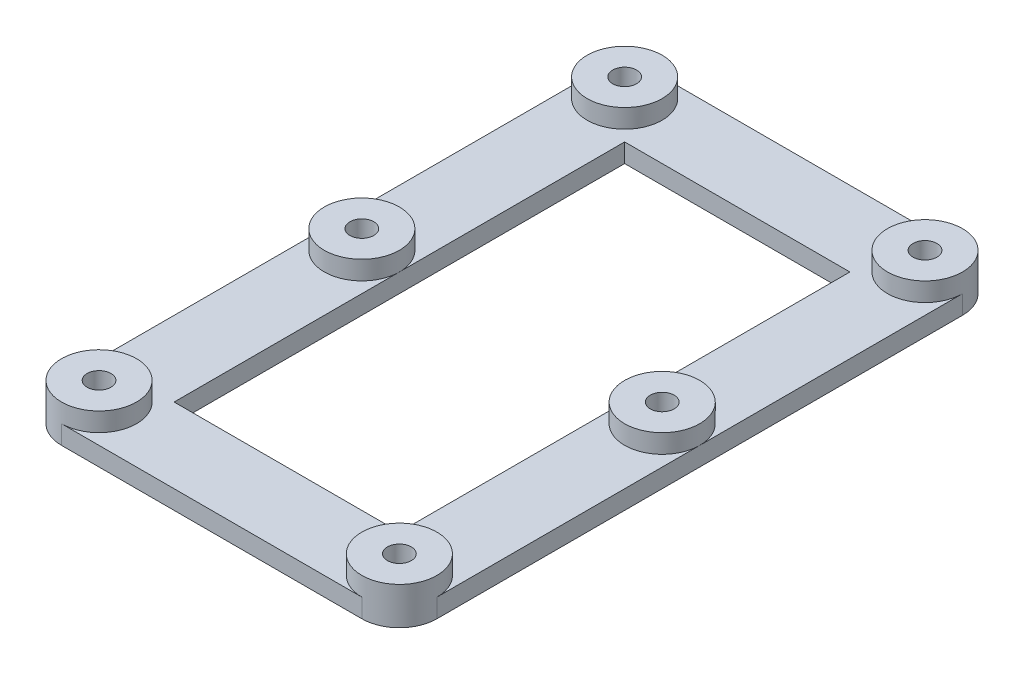
SolidWorks part; units mm, degrees
material "5052-H32"
ref_plane "Front Plane" through (0, 0, 0) normal (0, 0, 1) x (1, 0, 0)
ref_plane "Top Plane" through (0, 0, 0) normal (0, 1, 0) x (1, 0, 0)
ref_plane "Right Plane" through (0, 0, 0) normal (1, 0, 0) x (0, 0, -1)
sketch "Sketch1" plane through (0, 0, 0) normal (0, 1, 0) x (1, 0, 0)
  line L1 (31.75, -50.8) -> (-31.75, -50.8)
  line L2 (31.75, -50.8) -> (31.75, 50.8)
  line L3 (31.75, 50.8) -> (-31.75, 50.8)
  line L4 (-31.75, -50.8) -> (-31.75, 50.8)
  line L5 (31.75, -50.8) -> (-31.75, 50.8) construction
  line L6 (31.75, 50.8) -> (-31.75, -50.8) construction
  point P0 (0, 0)
  dimension "D1" = 101.6
  dimension "D2" = 63.5
extrude "Boss-Extrude1" add sketch "Sketch1" along normal blind 6.35
fillet "Fillet1" radius 6.35 4 edges at (31.75, 3.175, -50.8) (31.75, 3.175, 50.8) (-31.75, 3.175, 50.8) (-31.75, 3.175, -50.8)
hole_wizard "#10-32 Tapped Hole1" positions "Sketch8" profile "Sketch9" tap size "#10-32" standard "ANSI Inch" end condition through all
sketch "Sketch8" plane through (0, 6.35, 0) normal (0, 1, 0) x (1, 0, 0)
  line L0 (25.4, 44.45) -> (-25.4, 44.45)
  line L1 (-25.4, 44.45) -> (-25.4, -44.45)
  line L2 (-25.4, -44.45) -> (25.4, -44.45)
  line L3 (25.4, -44.45) -> (25.4, 44.45)
  point P1 (25.4, 44.45)
  point P2 (-25.4, 44.45)
  point P6 (-25.4, -44.45)
  point P9 (25.4, -44.45)
  point P23 (-25.4, 0)
  point P25 (25.4, 0)
sketch "Sketch9" plane through (25.4, 6.35, -44.45) normal (1, 0, 0) x (0, 0, 1)
  line L0 (0, 0) -> (0, 6.35)
  line L1 (0, 6.35) -> (2.0193, 6.35)
  line L2 (2.0193, 6.35) -> (2.0193, 0)
  line L5 (2.0193, 0) -> (0, 0)
  line L11 (0, -6.35) -> (0, 107.95) construction
  dimension "Thread Major Dia." = 4.0386
  dimension "Thru Tap Drill Depth" = 6.35
sketch "Sketch10" plane through (0, 6.35, 0) normal (0, 1, 0) x (1, 0, 0)
  line L0 (-31.75, 44.45) -> (-31.75, -44.45) construction
  line L1 (19.05, -38.1) -> (-19.05, -38.1)
  line L2 (19.05, -38.1) -> (19.05, 38.1)
  line L3 (19.05, 38.1) -> (-19.05, 38.1)
  line L4 (-19.05, -38.1) -> (-19.05, 38.1)
  line L5 (19.05, -38.1) -> (-19.05, 38.1) construction
  line L6 (19.05, 38.1) -> (-19.05, -38.1) construction
  line L7 (25.4, 50.8) -> (-25.4, 50.8) construction
  point P0 (0, 0)
  dimension "D1" = 12.7
  dimension "D2" = 12.7
extrude "Cut-Extrude1" cut sketch "Sketch10" against normal through all
sketch "Sketch11" plane through (0, 6.35, 0) normal (0, 1, 0) x (1, 0, 0)
  line L0 (-19.05, -38.1) -> (19.05, -38.1) construction
  line L1 (19.05, -38.1) -> (19.05, 38.1) construction
  line L2 (19.05, 38.1) -> (-19.05, 38.1) construction
  line L3 (-19.05, 38.1) -> (-19.05, -38.1) construction
  line L4 (31.75, -44.45) -> (31.75, 44.45)
  line L5 (25.4, 50.8) -> (-25.4, 50.8)
  line L6 (-31.75, 44.45) -> (-31.75, -44.45)
  line L7 (-25.4, -50.8) -> (25.4, -50.8)
  line L8 (31.75, -44.45) -> (31.75, 0)
  line L9 (25.4, 50.8) -> (-25.4, 50.8)
  line L10 (-31.75, 44.45) -> (-31.75, 0)
  line L11 (-25.4, -50.8) -> (25.4, -50.8)
  line L12 (-19.05, -38.1) -> (19.05, -38.1)
  line L13 (19.05, -38.1) -> (19.05, 0)
  line L14 (19.05, 38.1) -> (-19.05, 38.1)
  line L15 (-19.05, 38.1) -> (-19.05, 0)
  line L17 (-19.05, 0) -> (-19.05, -38.1)
  line L18 (-31.75, 0) -> (-31.75, -44.45)
  line L19 (19.05, 0) -> (19.05, 38.1)
  line L20 (31.75, 0) -> (31.75, 44.45)
  arc A0 (-31.75, 44.45) -> (-25.4, 50.8) centre (-25.4, 44.45) ccw
  arc A1 (-31.75, 0) -> (-19.05, 0) centre (-25.4, 0) ccw
  arc A2 (-25.4, -50.8) -> (-31.75, -44.45) centre (-25.4, -44.45) ccw
  arc A3 (31.75, -44.45) -> (25.4, -50.8) centre (25.4, -44.45) ccw
  arc A4 (19.05, 0) -> (31.75, 0) centre (25.4, 0) ccw
  arc A5 (25.4, 50.8) -> (31.75, 44.45) centre (25.4, 44.45) ccw
  arc A7 (-25.4, 50.8) -> (-31.75, 44.45) centre (-25.4, 44.45) ccw construction
  arc A8 (31.75, 44.45) -> (25.4, 50.8) centre (25.4, 44.45) ccw construction
  arc A9 (-31.75, -44.45) -> (-25.4, -50.8) centre (-25.4, -44.45) ccw construction
  arc A10 (31.75, 44.45) -> (25.4, 50.8) centre (25.4, 44.45) ccw
  arc A11 (-25.4, 50.8) -> (-31.75, 44.45) centre (-25.4, 44.45) ccw
  arc A12 (-31.75, -44.45) -> (-25.4, -50.8) centre (-25.4, -44.45) ccw
  arc A13 (25.4, -50.8) -> (31.75, -44.45) centre (25.4, -44.45) ccw
  arc A14 (25.4, 50.8) -> (31.75, 44.45) centre (25.4, 44.45) ccw
  arc A17 (25.4, -50.8) -> (31.75, -44.45) centre (25.4, -44.45) ccw
  arc A18 (-19.05, 0) -> (-31.75, 0) centre (-25.4, 0) ccw
  arc A19 (31.75, 0) -> (19.05, 0) centre (25.4, 0) ccw
  point P1 (-25.4, 50.8)
  point P8 (31.75, 43.1786)
  point P45 (-88.0996, -10.1577)
  point P47 (0, 0)
  point P48 (0, 0)
  point P49 (0, 0)
  point P51 (0, 0)
  line M22 (-19.05, -38.1) -> (-19.05, 38.1)
  line M23 (-19.05, 38.1) -> (19.05, 38.1)
  line M24 (19.05, 38.1) -> (19.05, -38.1)
  line M25 (19.05, -38.1) -> (-19.05, -38.1)
  line M32 (31.75, -44.45) -> (31.75, 44.45)
  line M34 (25.4, 50.8) -> (-25.4, 50.8)
  line M36 (-31.75, 44.45) -> (-31.75, -44.45)
  line M38 (-25.4, -50.8) -> (25.4, -50.8)
  dimension "D1" = 0
extrude "Cut-Extrude2" cut sketch "Sketch11" against normal blind 3.175 contours A4 A1 A2 A3 M24 M25 M22 M36 M38 M32 | A19 A5 A0 A18 M32 M34 M36 M22 M23 M24
